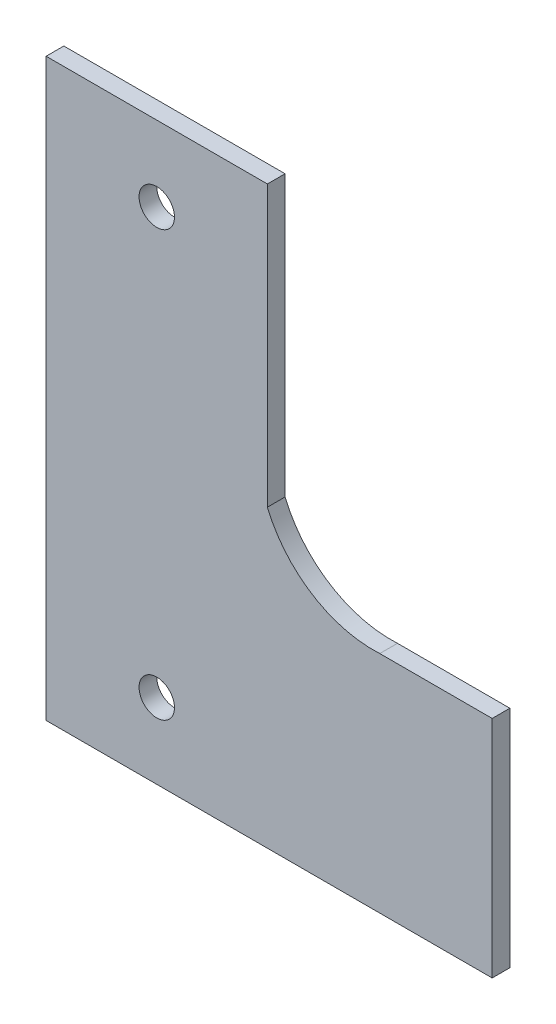
SolidWorks part; units mm, degrees
material "6061 Alloy"
ref_plane "Front Plane" through (0, 0, 0) normal (0, 0, 1) x (1, 0, 0)
ref_plane "Top Plane" through (0, 0, 0) normal (0, 1, 0) x (1, 0, 0)
ref_plane "Right Plane" through (0, 0, 0) normal (1, 0, 0) x (0, 0, -1)
sketch "Sketch1" plane through (0, 0, 0) normal (0, 0, 1) x (1, 0, 0)
  line L0 (35.163, 7.2401) -> (9.763, -18.1599) construction
  line L1 (-15.237, 46.8401) -> (9.763, -18.1599) construction
  line L2 (-15.237, 20.7757) -> (-15.237, -18.1599)
  line L3 (9.763, -18.1599) -> (-15.237, -18.1599)
  line L4 (9.763, 20.7757) -> (9.763, -18.1599)
  line L5 (9.763, 7.2401) -> (35.163, 7.2401)
  line L6 (9.763, 46.8401) -> (-15.237, -18.1599) construction
  line L7 (9.763, -18.1599) -> (35.163, -18.1599)
  line L8 (35.163, 7.2401) -> (35.163, -18.1599)
  line L10 (9.763, 7.2401) -> (35.163, -18.1599) construction
  line L11 (-15.237, 20.7757) -> (-15.237, 46.8401)
  line L12 (-15.237, 46.8401) -> (9.763, 46.8401)
  line L13 (9.763, 46.8401) -> (9.763, 20.7757)
  arc A1 (22.463, 7.2401) -> (9.763, 15.2101) centre (21.7242, 20.1663) cw
  circle A2 centre (-2.737, 38.3401) radius 2
  circle A3 centre (-2.737, -9.6599) radius 2
  point P1 (-2.737, 14.3401)
  point P9 (22.463, -5.4599)
  point P10 (22.463, 20.7757)
  point P11 (22.463, -31.6955)
  dimension "D6" = 4
  dimension "D7" = 4
  dimension "D1" = 65
  dimension "D2" = 24
  dimension "D3" = 25.4
  dimension "D4" = 25.4
  dimension "D8" = 48
extrude "Boss-Extrude1" add sketch "Sketch1" along normal blind 2
